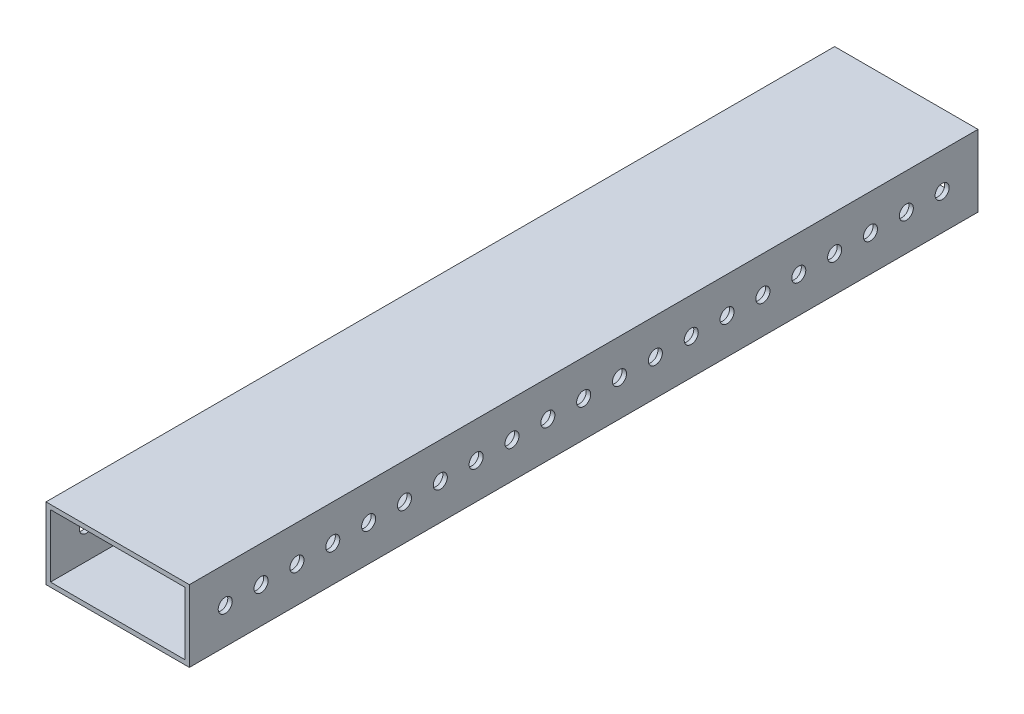
SolidWorks part; units mm, degrees
material "6061 Alloy"
ref_plane "Front Plane" through (0, 0, 0) normal (0, 0, 1) x (1, 0, 0)
ref_plane "Top Plane" through (0, 0, 0) normal (0, 1, 0) x (1, 0, 0)
ref_plane "Right Plane" through (0, 0, 0) normal (1, 0, 0) x (0, 0, -1)
sketch "Sketch1" plane through (0, 0, 0) normal (0, 0, 1) x (1, 0, 0)
  line L0 (1.5875, 1.5875) -> (49.2125, 1.5875)
  line L1 (0, 0) -> (50.8, 0)
  line L2 (0, 0) -> (0, 25.4)
  line L3 (0, 25.4) -> (50.8, 25.4)
  line L4 (50.8, 0) -> (50.8, 25.4)
  line L5 (49.2125, 1.5875) -> (49.2125, 23.8125)
  line L6 (1.5875, 23.8125) -> (49.2125, 23.8125)
  line L7 (1.5875, 1.5875) -> (1.5875, 23.8125)
  dimension "D1" = 25.4
  dimension "D2" = 50.8
  dimension "D3" = 1.5875
extrude "Boss-Extrude1" add sketch "Sketch1" along normal blind 279.4
sketch "Sketch2" plane through (50.8, 0, 0) normal (1, 0, 0) x (0, 0, -1)
  line L0 (-279.4, 0) -> (-279.4, 25.4) construction
  line L1 (-266.7, 12.7) -> (-254, 12.7) construction
  circle A0 centre (-266.7, 12.7) radius 2.4892
  circle A1 centre (-254, 12.7) radius 2.4892
  circle A2 centre (-241.3, 12.7) radius 2.4892
  circle A3 centre (-228.6, 12.7) radius 2.4892
  circle A4 centre (-215.9, 12.7) radius 2.4892
  circle A5 centre (-203.2, 12.7) radius 2.4892
  circle A6 centre (-190.5, 12.7) radius 2.4892
  circle A7 centre (-177.8, 12.7) radius 2.4892
  circle A8 centre (-165.1, 12.7) radius 2.4892
  circle A9 centre (-152.4, 12.7) radius 2.4892
  circle A10 centre (-139.7, 12.7) radius 2.4892
  circle A11 centre (-127, 12.7) radius 2.4892
  circle A12 centre (-114.3, 12.7) radius 2.4892
  circle A13 centre (-101.6, 12.7) radius 2.4892
  circle A14 centre (-88.9, 12.7) radius 2.4892
  circle A15 centre (-76.2, 12.7) radius 2.4892
  circle A16 centre (-63.5, 12.7) radius 2.4892
  circle A17 centre (-50.8, 12.7) radius 2.4892
  circle A18 centre (-38.1, 12.7) radius 2.4892
  circle A19 centre (-25.4, 12.7) radius 2.4892
  circle A20 centre (-12.7, 12.7) radius 2.4892
  point P4 (-279.4, 12.7)
  dimension "D1" = 4.9784
  dimension "D2" = 12.7
  dimension "D4" = 12.7
  dimension "D3" = 21
extrude "Cut-Extrude1" cut sketch "Sketch2" against normal through all
